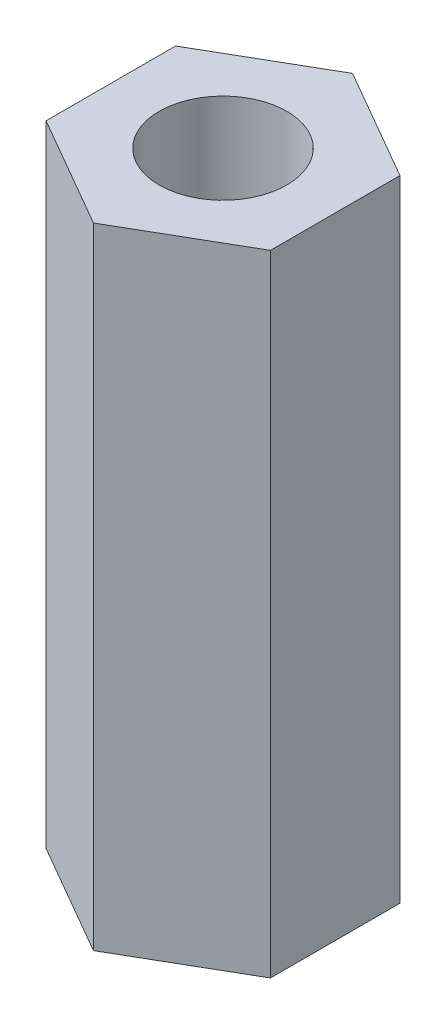
SolidWorks part; units mm, degrees
ref_plane "Спереди" through (0, 0, 0) normal (0, 0, 1) x (1, 0, 0)
ref_plane "Сверху" through (0, 0, 0) normal (0, 1, 0) x (1, 0, 0)
ref_plane "Справа" through (0, 0, 0) normal (1, 0, 0) x (0, 0, -1)
sketch "Эскиз1" plane through (0, 0, 0) normal (0, 1, 0) x (1, 0, 0)
  line L1 (0, 3.0426) -> (-2.635, 1.5213)
  line L2 (-2.635, 1.5213) -> (-2.635, -1.5213)
  line L3 (-2.635, -1.5213) -> (0, -3.0426)
  line L4 (0, -3.0426) -> (2.635, -1.5213)
  line L5 (2.635, -1.5213) -> (2.635, 1.5213)
  line L6 (2.635, 1.5213) -> (0, 3.0426)
  circle A0 centre (0, 0) radius 2.635 construction
  circle A1 centre (0, 0) radius 1.5
  dimension "D1" = 3
  dimension "D2" = 5.27
extrude "Бобышка-Вытянуть1" add sketch "Эскиз1" along normal blind 14.8
